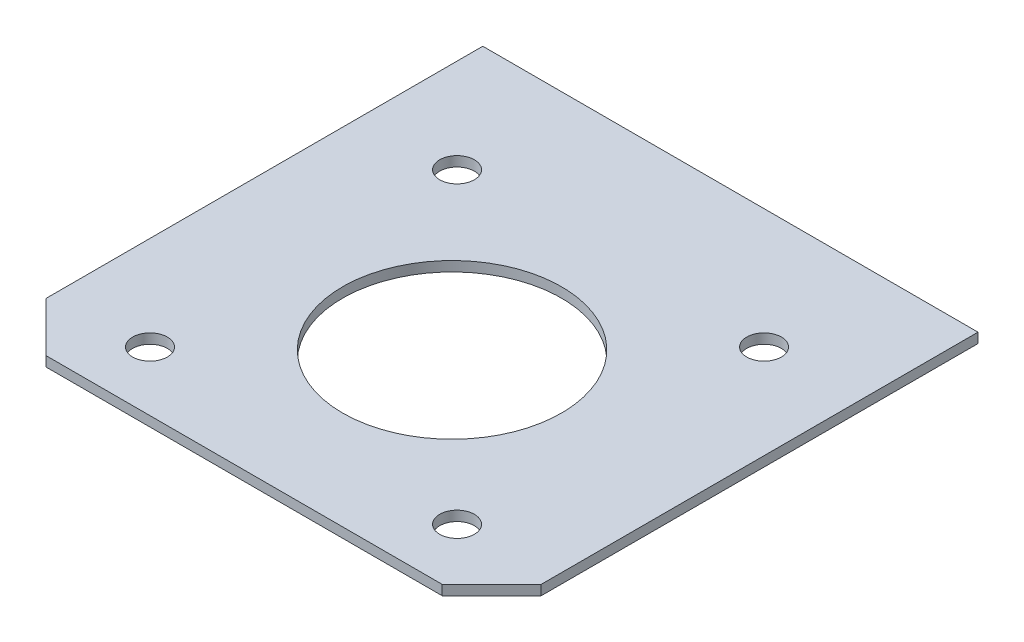
SolidWorks part; units mm, degrees
ref_plane "Alzado" through (0, 0, 0) normal (0, 0, 1) x (1, 0, 0)
ref_plane "Planta" through (0, 0, 0) normal (0, 1, 0) x (1, 0, 0)
ref_plane "Vista lateral" through (0, 0, 0) normal (1, 0, 0) x (0, 0, -1)
sketch "Sketch1" plane through (0, 0, 0) normal (0, 1, 0) x (1, 0, 0)
  line L0 (0, -245.5) -> (0, -35.5) construction
  line L1 (-250, -245.5) -> (250, -245.5)
  line L2 (-250, -245.5) -> (-250, 245.5)
  line L3 (-250, 245.5) -> (250, 245.5)
  line L4 (250, -245.5) -> (250, 245.5)
  line L5 (-250, -245.5) -> (250, 245.5) construction
  line L6 (-250, 245.5) -> (250, -245.5) construction
  line L7 (-250, 245.5) -> (-250, 124.5) construction
  line L8 (0, 245.5) -> (-155, 245.5) construction
  line L9 (-250, 245.5) -> (-155, 124.5) construction
  line L10 (0, 245.5) -> (0, -245.5) construction
  line L11 (-155, 124.5) -> (155, 124.5) construction
  line L12 (-155, 124.5) -> (-155, -185.5) construction
  circle A0 centre (0, -35.5) radius 110.5
  circle A1 centre (-155, 124.5) radius 17.5
  circle A2 centre (155, 124.5) radius 17.5
  circle A3 centre (-155, -185.5) radius 17.5
  circle A4 centre (155, -185.5) radius 17.5
  point P0 (0, 0)
  dimension "D4" = 121
  dimension "D1" = 500
  dimension "D2" = 491
  dimension "D3" = 210
  dimension "D5" = 155
extrude "Boss-Extrude1" add sketch "Sketch1" along normal blind 10
chamfer "Chamfer1" distance 50 angle 45 2 edges at (250, 5, 245.5) (-250, 5, 245.5)
